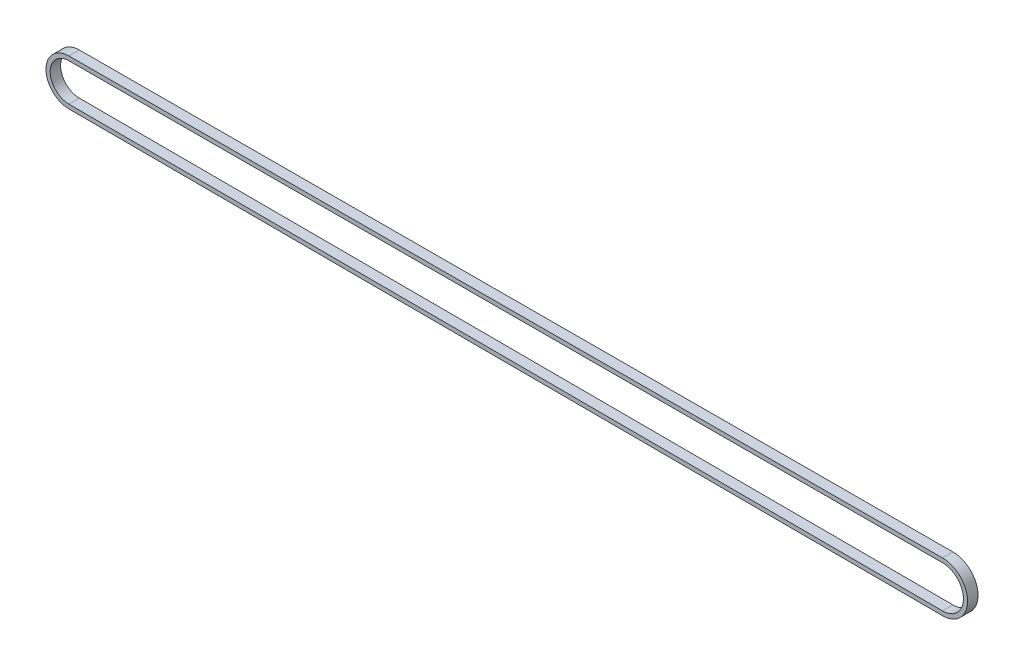
SolidWorks part; units mm, degrees
ref_plane "Front Plane" through (0, 0, 0) normal (0, 0, 1) x (1, 0, 0)
ref_plane "Top Plane" through (0, 0, 0) normal (0, 1, 0) x (1, 0, 0)
ref_plane "Right Plane" through (0, 0, 0) normal (1, 0, 0) x (0, 0, -1)
sketch "Sketch2" plane through (0, 0, 0) normal (0, 0, 1) x (1, 0, 0)
  line L0 (0, 0) -> (1, 0) construction
  line L1 (0, 0) -> (0, 1) construction
  line L2 (-0.0239, -10) -> (-419.0215, -9)
  line L3 (-419.0215, 9) -> (-0.0239, 10)
  arc A0 (-0.0239, 10) -> (-0.0239, -10) centre (0, 0) cw
  arc A1 (-419.0215, -9) -> (-419.0215, 9) centre (-419, 0) cw
extrude "Extrude-Thin1" add sketch "Sketch2" against normal blind 5 thin thin type one direction wall 2
